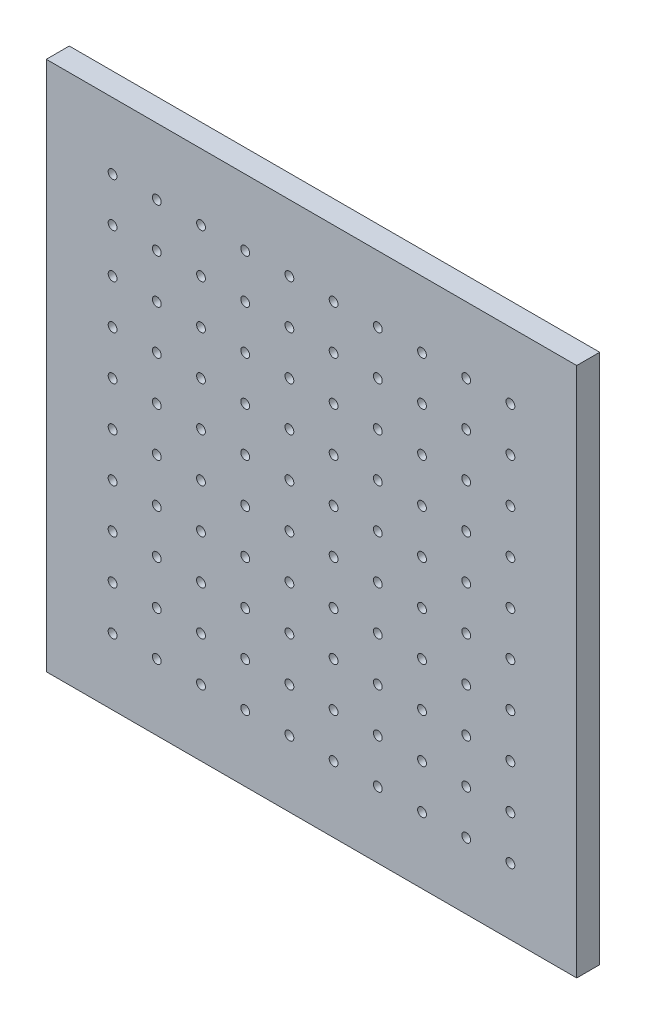
SolidWorks part; units mm, degrees
ref_plane "前视基准面" through (0, 0, 0) normal (0, 0, 1) x (1, 0, 0)
ref_plane "上视基准面" through (0, 0, 0) normal (0, 1, 0) x (1, 0, 0)
ref_plane "右视基准面" through (0, 0, 0) normal (1, 0, 0) x (0, 0, -1)
sketch "草图1" plane through (0, 0, 0) normal (0, 0, 1) x (1, 0, 0)
  line L1 (-150, 150) -> (150, 150)
  line L2 (-150, 150) -> (-150, -150)
  line L3 (-150, -150) -> (150, -150)
  line L4 (150, 150) -> (150, -150)
  line L5 (-150, 150) -> (150, -150) construction
  line L6 (-150, -150) -> (150, 150) construction
  point P0 (0, 0)
  dimension "D1" = 300
  dimension "D2" = 300
extrude "凸台-拉伸1" add sketch "草图1" along normal blind 13
sketch "草图2" plane through (0, 0, 13) normal (0, 0, 1) x (1, 0, 0)
  line L0 (150, 150) -> (-150, 150) construction
  line L1 (-112.5, 112.5) -> (112.5, 112.5) construction
  line L2 (-112.5, 112.5) -> (-112.5, -112.5) construction
  line L3 (-112.5, -112.5) -> (112.5, -112.5) construction
  line L4 (112.5, 112.5) -> (112.5, -112.5) construction
  line L5 (-112.5, 112.5) -> (112.5, -112.5) construction
  line L6 (-112.5, -112.5) -> (112.5, 112.5) construction
  line L7 (150, -150) -> (150, 150) construction
  point P0 (0, 0)
  dimension "D1" = 37.5
  dimension "D2" = 37.5
hole_wizard "M6 螺纹孔的螺纹孔钻头1" positions "草图3" profile "草图4" hole size "M6" standard "DIN" end condition through all
sketch "草图3" plane through (0, 0, 13) normal (0, 0, 1) x (1, 0, 0)
  point P0 (-112.5, -112.5)
sketch "草图4" plane through (-112.5, -112.5, 13) normal (1, 0, 0) x (0, -1, 0)
  line L0 (0, 0) -> (0, 13)
  line L1 (0, 13) -> (2.5, 13)
  line L2 (2.5, 13) -> (2.5, 0)
  line L5 (2.5, 0) -> (0, 0)
  line L11 (0, -6.35) -> (0, 107.95) construction
  dimension "通孔孔直径" = 5
  dimension "通孔孔深度" = 13
pattern_linear "阵列(线性)1" count 10 spacing 25 along (0, 1, 0) count 10 spacing 25 along (1, 0, 0) of "M6 螺纹孔的螺纹孔钻头1"
